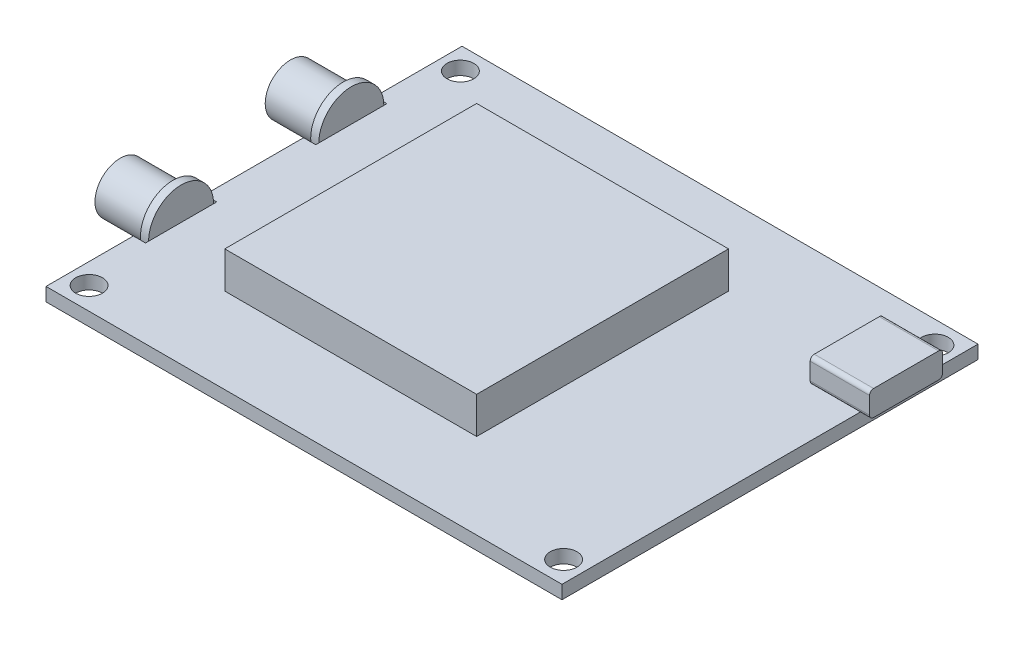
SolidWorks part; units mm, degrees
ref_plane "Front Plane" through (0, 0, 0) normal (0, 0, 1) x (1, 0, 0)
ref_plane "Top Plane" through (0, 0, 0) normal (0, 1, 0) x (1, 0, 0)
ref_plane "Right Plane" through (0, 0, 0) normal (1, 0, 0) x (0, 0, -1)
sketch "Sketch1" plane through (0, 0, 0) normal (0, 1, 0) x (1, 0, 0)
  line L1 (-33.6176, 19.9427) -> (29.8824, 19.9427)
  line L2 (-33.6176, 19.9427) -> (-33.6176, -31.2573)
  line L3 (-33.6176, -31.2573) -> (29.8824, -31.2573)
  line L4 (29.8824, 19.9427) -> (29.8824, -31.2573)
  dimension "D1" = 63.5
  dimension "D2" = 51.2
extrude "Boss-Extrude1" add sketch "Sketch1" along normal blind 1.65
sketch "Sketch2" plane through (0, 1.65, 0) normal (0, 1, 0) x (1, 0, 0)
  line L0 (-33.6176, 19.9427) -> (-33.6176, -31.2573) construction
  line L1 (-22.1176, 10.2427) -> (8.8824, 10.2427)
  line L2 (-22.1176, 10.2427) -> (-22.1176, -20.7573)
  line L3 (-22.1176, -20.7573) -> (8.8824, -20.7573)
  line L4 (8.8824, 10.2427) -> (8.8824, -20.7573)
  line L5 (-33.6176, -31.2573) -> (29.8824, -31.2573) construction
  point P6 (-33.6176, -5.6573)
  dimension "D1" = 11.5
  dimension "D2" = 10.5
  dimension "D3" = 31
  dimension "D4" = 31
extrude "Boss-Extrude2" add sketch "Sketch2" along normal blind 4.5
sketch "Sketch3" plane through (-33.6176, 0, 0) normal (-1, 0, 0) x (0, 0, 1)
  line L0 (-19.9427, 1.65) -> (31.2573, 1.65) construction
  line L1 (-9.1927, 1.65) -> (-0.4427, 1.65)
  line L2 (-9.1927, 1.65) -> (-9.1927, 0)
  line L3 (-9.1927, 0) -> (-0.4427, 0)
  line L4 (-0.4427, 1.65) -> (-0.4427, 0)
  line L5 (28.16, 0) -> (-28.16, 0) construction
  line L6 (-19.9427, 1.65) -> (-19.9427, 0) construction
  line L7 (5.6573, 1.65) -> (5.6573, 0) construction
  line L8 (20.5073, 0) -> (11.7573, 0)
  line L9 (11.7573, 1.65) -> (11.7573, 0)
  line L10 (20.5073, 1.65) -> (11.7573, 1.65)
  line L11 (20.5073, 1.65) -> (20.5073, 0)
  dimension "D1" = 8.75
  dimension "D2" = 10.75
extrude "Cut-Extrude1" cut sketch "Sketch3" against normal blind 1.5
ref_plane "Plane1" through (-32.1176, 0, 0) normal (-1, 0, 0) x (0, 0, 1)
sketch "Sketch4" plane through (-32.1176, 0, 0) normal (-1, 0, 0) x (0, 0, 1)
  line L0 (-9.1927, 1.65) -> (-0.4427, 1.65) construction
  circle A0 centre (-4.8177, 1.65) radius 4
  dimension "D1" = 8
extrude "Boss-Extrude3" add sketch "Sketch4" along normal blind 1 contours A0
sketch "Sketch5" plane through (-33.1176, 0, 0) normal (-1, 0, 0) x (0, 0, 1)
  circle A0 centre (-4.8177, 1.65) radius 3.1
  dimension "D1" = 6.2
extrude "Boss-Extrude4" add sketch "Sketch5" along normal blind 6.5
ref_plane "Plane2" through (0, 0, 5.6573) normal (0, 0, -1) x (-1, 0, 0)
mirror "Mirror1" about plane through (0, 0, 5.6573) normal (0, 0, -1) of "Boss-Extrude4", "Boss-Extrude3"
sketch "Sketch6" plane through (0, 1.65, 0) normal (0, 1, 0) x (1, 0, 0)
  line L0 (-33.6176, 19.9427) -> (-32.7176, 19.9427) construction
  line L1 (29.8824, 19.9427) -> (-33.6176, 19.9427) construction
  line L2 (-33.6176, 19.9427) -> (-33.6176, 9.1927) construction
  line L3 (-1.8676, 19.9427) -> (-1.8676, -31.2573) construction
  line L4 (-33.6176, -31.2573) -> (29.8824, -31.2573) construction
  line L5 (-33.6176, -5.6573) -> (29.8824, -5.6573) construction
  line L6 (-33.6176, 0.4427) -> (-33.6176, -11.7573) construction
  line L7 (29.8824, -31.2573) -> (29.8824, 19.9427) construction
  circle A0 centre (-31.0676, 17.1927) radius 1.65
  circle A1 centre (-31.0676, -28.5073) radius 1.65
  circle A2 centre (27.3324, -28.5073) radius 1.65
  circle A3 centre (27.3324, 17.1927) radius 1.65
  dimension "D1" = 3.3
  dimension "D2" = 2.55
  dimension "D3" = 2.75
extrude "Cut-Extrude2" cut sketch "Sketch6" against normal up to surface (1.65 mm away) and the other way through all up to face at (-24.9301, 0, 5.6573)
ref_plane "Plane3" through (23.9824, 0, 0) normal (1, 0, 0) x (0, 0, -1)
sketch "Sketch7" plane through (23.9824, 0, 0) normal (1, 0, 0) x (0, 0, -1)
  line L0 (19.9427, 1.65) -> (14.1927, 1.65) construction
  line L1 (-31.2573, 1.65) -> (19.9427, 1.65) construction
  line L3 (13.6927, 1.65) -> (5.6927, 1.65)
  line L4 (14.1927, 2.15) -> (14.1927, 4.25)
  line L5 (13.6927, 4.75) -> (5.6927, 4.75)
  line L6 (5.1927, 2.15) -> (5.1927, 4.25)
  arc A0 (13.6927, 1.65) -> (14.1927, 2.15) centre (13.6927, 2.15) ccw
  arc A1 (5.6927, 1.65) -> (5.1927, 2.15) centre (5.6927, 2.15) cw
  arc A2 (13.6927, 4.75) -> (14.1927, 4.25) centre (13.6927, 4.25) cw
  arc A3 (5.6927, 4.75) -> (5.1927, 4.25) centre (5.6927, 4.25) ccw
  point P13 (5.1927, 1.65)
  point P16 (14.1927, 4.75)
  point P19 (5.1927, 4.75)
  dimension "D4" = 0.5
  dimension "D1" = 5.75
  dimension "D2" = 9
  dimension "D3" = 3.1
extrude "Boss-Extrude5" add sketch "Sketch7" along normal blind 7.3 contours A3 L5 A2 L4 A0 L3 A1 L6
